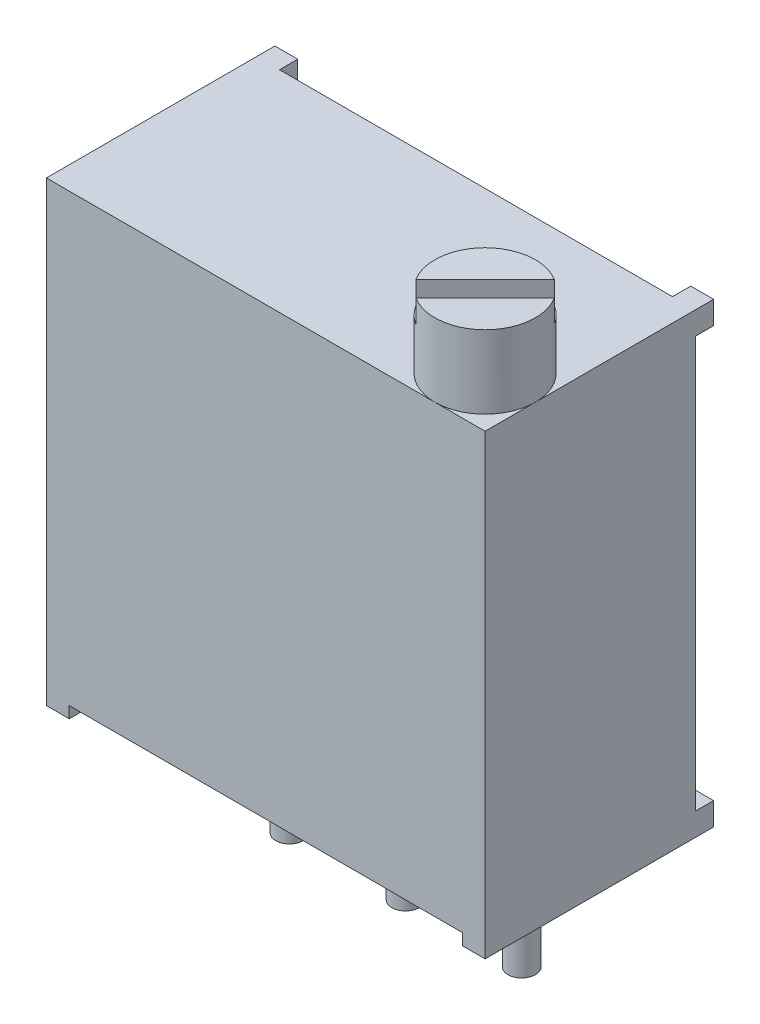
SolidWorks part; units mm, degrees
ref_plane "Front Plane" through (0, 0, 0) normal (0, 0, 1) x (1, 0, 0)
ref_plane "Top Plane" through (0, 0, 0) normal (0, 1, 0) x (1, 0, 0)
ref_plane "Right Plane" through (0, 0, 0) normal (1, 0, 0) x (0, 0, -1)
sketch "Component_Outline" plane through (0, 0, 0) normal (0, 1, 0) x (1, 0, 0)
  line L1 (2.2, 2) -> (-7.4, 2)
  line L2 (2.2, 2) -> (2.2, -3)
  line L3 (2.2, -3) -> (-7.4, -3)
  line L4 (-7.4, 2) -> (-7.4, -3)
  point P7 (3.4953, -0.0862)
  dimension "D1" = 5
  dimension "D2" = 9.6
  dimension "D3" = 3
  dimension "D4" = 2.2
sketch3d "3DSketch1"
  line L0 (0, 0, 0) -> (1, 0, 0)
  line L1 (0, 0, 0) -> (0, 0, -1)
  line L2 (0, 0, 0) -> (0, 1, 0)
  point P0 (0, 0, 0)
extrude "Boss-Extrude1" add sketch "Component_Outline" along normal blind 10
sketch "Sketch1" plane through (0, 0, -2) normal (0, 0, -1) x (-1, 0, 0)
  line L1 (7.4, 10) -> (6.9, 10)
  line L2 (7.4, 10) -> (7.4, 9.5)
  line L3 (7.4, 9.5) -> (6.9, 9.5)
  line L4 (6.9, 10) -> (6.9, 9.5)
  line L5 (-2.2, 10) -> (-1.7, 10)
  line L6 (-2.2, 10) -> (-2.2, 9.5)
  line L7 (-2.2, 9.5) -> (-1.7, 9.5)
  line L8 (-1.7, 10) -> (-1.7, 9.5)
  line L9 (-2.2, 0) -> (-1.7, 0)
  line L10 (-2.2, 0) -> (-2.2, 0.5)
  line L11 (-2.2, 0.5) -> (-1.7, 0.5)
  line L12 (-1.7, 0) -> (-1.7, 0.5)
  line L13 (7.4, 0) -> (6.9, 0)
  line L14 (7.4, 0) -> (7.4, 0.5)
  line L15 (7.4, 0.5) -> (6.9, 0.5)
  line L16 (6.9, 0) -> (6.9, 0.5)
  dimension "D1" = 0.5
extrude "Cut-Extrude1" cut sketch "Sketch1" against normal blind 0.4 flip side to cut
sketch "Sketch2" plane through (0, 0, 0) normal (0, -1, 0) x (1, 0, 0)
  line L0 (-7.4, 3) -> (2.2, 3) construction
  line L1 (-6.9, -1.6) -> (1.7, -1.6)
  line L2 (-6.9, -1.6) -> (-6.9, 3)
  line L3 (-6.9, 3) -> (1.7, 3)
  line L4 (1.7, -1.6) -> (1.7, 3)
extrude "Cut-Extrude2" cut sketch "Sketch2" against normal blind 0.25
sketch "Sketch3" plane through (0, 0.25, 0) normal (0, -1, 0) x (1, 0, 0)
  line L0 (0, 0) -> (-2.54, 0) construction
  line L1 (-2.54, 0) -> (-5.08, 0) construction
  circle A0 centre (0, 0) radius 0.3
  circle A1 centre (-2.54, 0) radius 0.3
  circle A2 centre (-5.08, 0) radius 0.3
  dimension "D1" = 0.6
  dimension "D2" = 2.54
extrude "Boss-Extrude2" add sketch "Sketch3" along normal blind 3
sketch "Sketch4" plane through (0, 10, 0) normal (0, 1, 0) x (1, 0, 0)
  line L0 (-7.4, -3) -> (2.2, -3) construction
  line L1 (2.2, -3) -> (2.2, 2) construction
  circle A0 centre (1.1, -1.9) radius 1.1
  dimension "D1" = 2.2
extrude "Boss-Extrude3" add sketch "Sketch4" along normal blind 1.6 separate body
sketch "Sketch5" plane through (0, 11.6, 0) normal (0, 1, 0) x (1, 0, 0)
  line L0 (1.1, -1.9) -> (1.8778, -1.1222) construction
  line L1 (1.1, -1.9) -> (0.3222, -2.6778) construction
  line L2 (1.1, -1.9) -> (2.2, -1.9) construction
  line L3 (0.1658, -2.4807) -> (1.6807, -0.9658)
  line L4 (2.0342, -1.3193) -> (0.5193, -2.8342)
  circle A0 centre (1.1, -1.9) radius 1.1 construction
  arc A1 (0.1658, -2.4807) -> (0.5193, -2.8342) centre (1.1, -1.9) ccw
  arc A2 (2.0342, -1.3193) -> (1.6807, -0.9658) centre (1.1, -1.9) ccw
  dimension "D1" = 45
  dimension "D2" = 0.5
extrude "Cut-Extrude3" cut sketch "Sketch5" against normal blind 0.5
